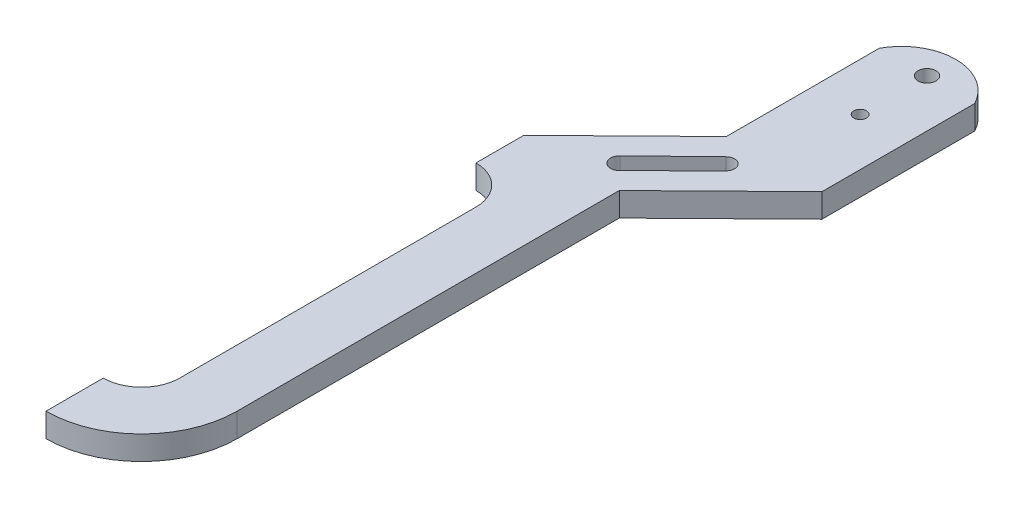
SolidWorks part; units mm, degrees
ref_plane "Front Plane" through (0, 0, 0) normal (0, 0, 1) x (1, 0, 0)
ref_plane "Top Plane" through (0, 0, 0) normal (0, 1, 0) x (1, 0, 0)
ref_plane "Right Plane" through (0, 0, 0) normal (1, 0, 0) x (0, 0, -1)
sketch "Sketch1" plane through (0, 0, 0) normal (0, 1, 0) x (1, 0, 0)
  line L0 (-0.9044, -38.735) -> (-0.9044, -89.535)
  line L1 (0, -25.4) -> (-13.6044, -38.735)
  line L2 (0, -5.08) -> (0, -25.4)
  line L3 (-13.6044, -38.735) -> (-13.6044, -45.085)
  line L4 (12.7, -25.4) -> (-0.9044, -38.735)
  line L5 (-8.5244, -50.165) -> (-8.5244, -89.535)
  line L8 (-3.1703, -36.4234) -> (3.9171, -29.3962)
  line L9 (2.3059, -27.7525) -> (-4.8566, -34.6931)
  line L10 (12.7, -25.4) -> (12.7, -5.08)
  line L11 (-13.6044, -94.615) -> (-13.6044, -102.235)
  arc A0 (3.9171, -29.3962) -> (2.3059, -27.7525) centre (3.1115, -28.5744) ccw
  circle A1 centre (6.35, -5.08) radius 1.1906
  arc A2 (-0.9044, -89.535) -> (-13.6044, -102.235) centre (-13.6044, -89.535) cw
  arc A3 (-13.6044, -45.085) -> (-8.5244, -50.165) centre (-13.6044, -50.165) cw
  arc A4 (-8.5244, -89.535) -> (-13.6044, -94.615) centre (-13.6044, -89.535) cw
  arc A5 (-3.1703, -36.4234) -> (-4.8566, -34.6931) centre (-4.0159, -35.5606) cw
  arc A6 (6.35, -1.27) -> (12.7, -5.08) centre (6.35, -8.4667) cw
  circle A7 centre (6.35, -13.97) radius 0.8401
  arc A8 (6.35, -1.27) -> (0, -5.08) centre (6.35, -8.4667) ccw
  dimension "D5" = 8.89
  dimension "D6" = 12.7
  dimension "D2" = 39.37
  dimension "D3" = 2.3813
  dimension "D14" = 6.35
  dimension "D15" = 1.6802
  dimension "D16" = 19.05
  dimension "D18" = 8.89
  dimension "D4" = 50.8
  dimension "D7" = 5.08
  dimension "D9" = 5.08
  dimension "D8" = 7.62
  dimension "D17" = 19.05
extrude "Boss-Extrude1" add sketch "Sketch1" along normal blind 3.175
